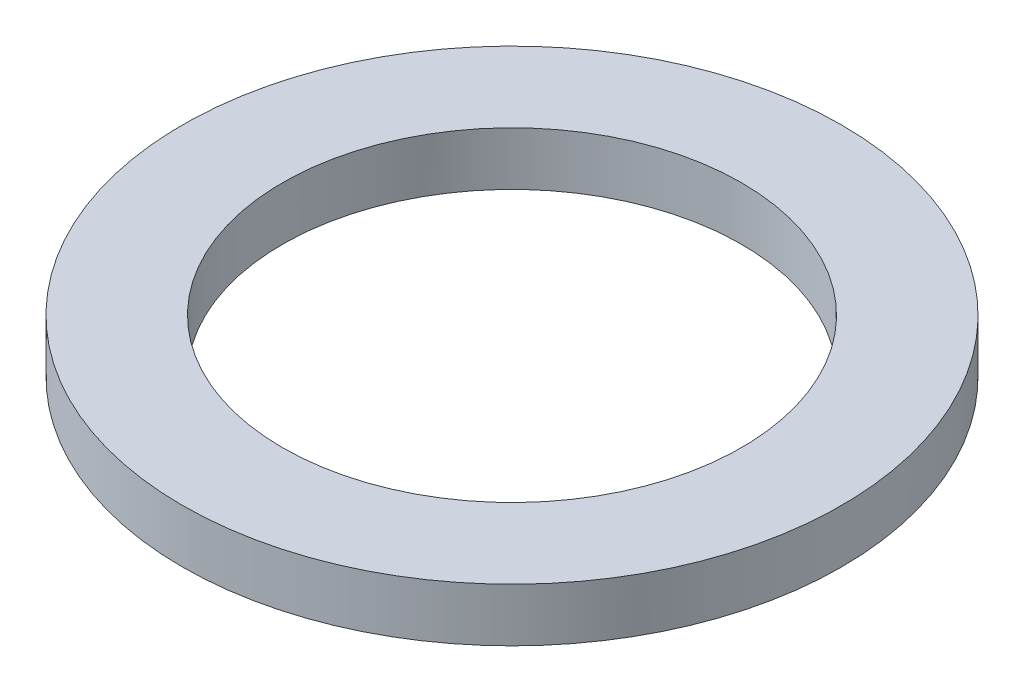
SolidWorks part; units mm, degrees
material "AISI 1020"
ref_plane "Спереди" through (0, 0, 0) normal (0, 0, 1) x (1, 0, 0)
ref_plane "Сверху" through (0, 0, 0) normal (0, 1, 0) x (1, 0, 0)
ref_plane "Справа" through (0, 0, 0) normal (1, 0, 0) x (0, 0, -1)
sketch "Эскиз1" plane through (0, 0, 0) normal (0, 1, 0) x (1, 0, 0)
  circle A3 centre (0, 0) radius 21.5
  circle A5 centre (0, 0) radius 30.874
  circle A6 centre (0, 0) radius 30.874
  dimension "D1" = 43
  dimension "D2" = 0.5
extrude "Бобышка-Вытянуть1" add sketch "Эскиз1" against normal up to surface (5 mm away)
